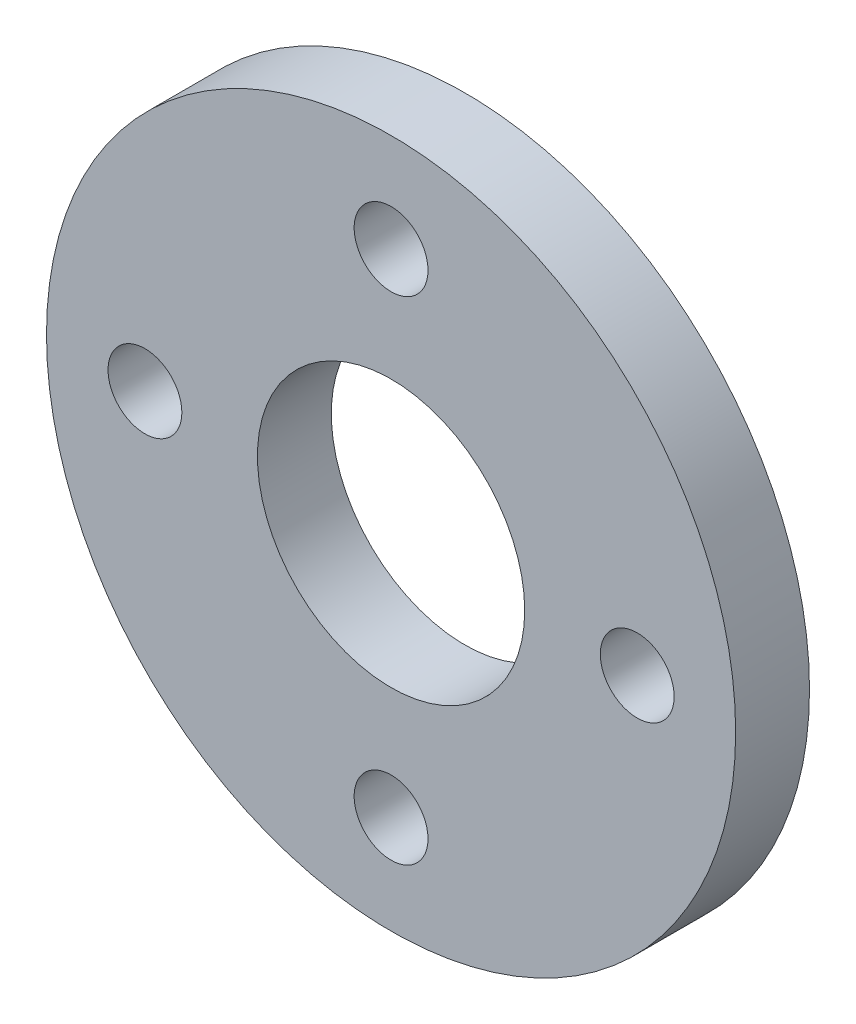
SolidWorks part; units mm, degrees
ref_plane "Front Plane" through (0, 0, 0) normal (0, 0, 1) x (1, 0, 0)
ref_plane "Top Plane" through (0, 0, 0) normal (0, 1, 0) x (1, 0, 0)
ref_plane "Right Plane" through (0, 0, 0) normal (1, 0, 0) x (0, 0, -1)
sketch "Sketch1" plane through (0, 0, 0) normal (0, 0, 1) x (1, 0, 0)
  circle A0 centre (0, 0) radius 355.6
  circle A2 centre (0, 0) radius 137.9128
  circle A3 centre (0, 254) radius 38.1
  circle A4 centre (254, 0) radius 38.1
  circle A5 centre (0, -254) radius 38.1
  circle A6 centre (-254, 0) radius 38.1
  point P16 (0, 0)
  dimension "D1" = 4
extrude "Boss-Extrude1" add sketch "Sketch1" along normal blind 76.2
